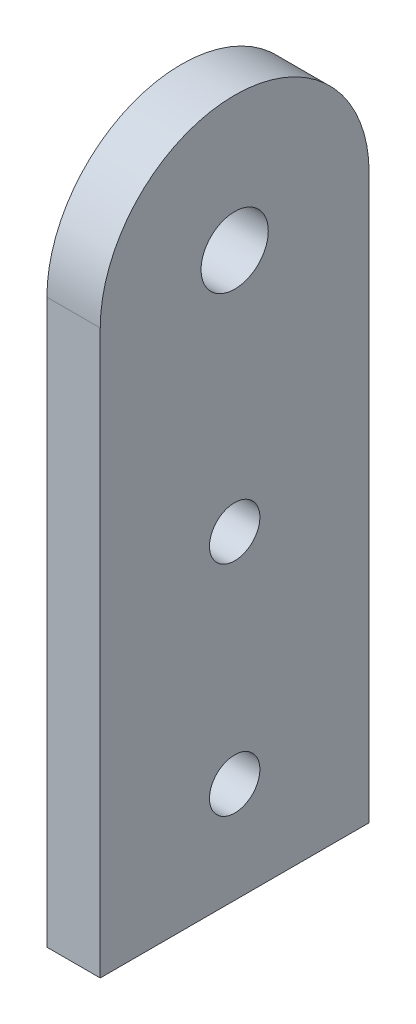
SolidWorks part; units mm, degrees
ref_plane "Front Plane" through (0, 0, 0) normal (0, 0, 1) x (1, 0, 0)
ref_plane "Top Plane" through (0, 0, 0) normal (0, 1, 0) x (1, 0, 0)
ref_plane "Right Plane" through (0, 0, 0) normal (1, 0, 0) x (0, 0, -1)
sketch "Sketch1" plane through (0, 0, 0) normal (1, 0, 0) x (0, 0, -1)
  line L0 (-8, 0) -> (-8, -33.5)
  line L1 (-8, -33.5) -> (8, -33.5)
  line L2 (8, -33.5) -> (8, 0)
  line L3 (0, 8) -> (0, -33.5) construction
  line L4 (-8, -14.5) -> (8, -14.5) construction
  line L5 (-8, -27.5) -> (8, -27.5) construction
  line L6 (-8, 0) -> (8, 0) construction
  circle A0 centre (0, 0) radius 8 construction
  arc A1 (-8, 0) -> (8, 0) centre (0, 0) cw
  circle A2 centre (0, 0) radius 2
  circle A3 centre (0, -14.5) radius 1.5
  circle A4 centre (0, -27.5) radius 1.5
  dimension "D1" = 16
  dimension "D2" = 4
  dimension "D6" = 3
  dimension "D7" = 3
  dimension "D3" = 14.5
  dimension "D4" = 13
  dimension "D5" = 6
extrude "Boss-Extrude1" add sketch "Sketch1" along normal blind 3.175
